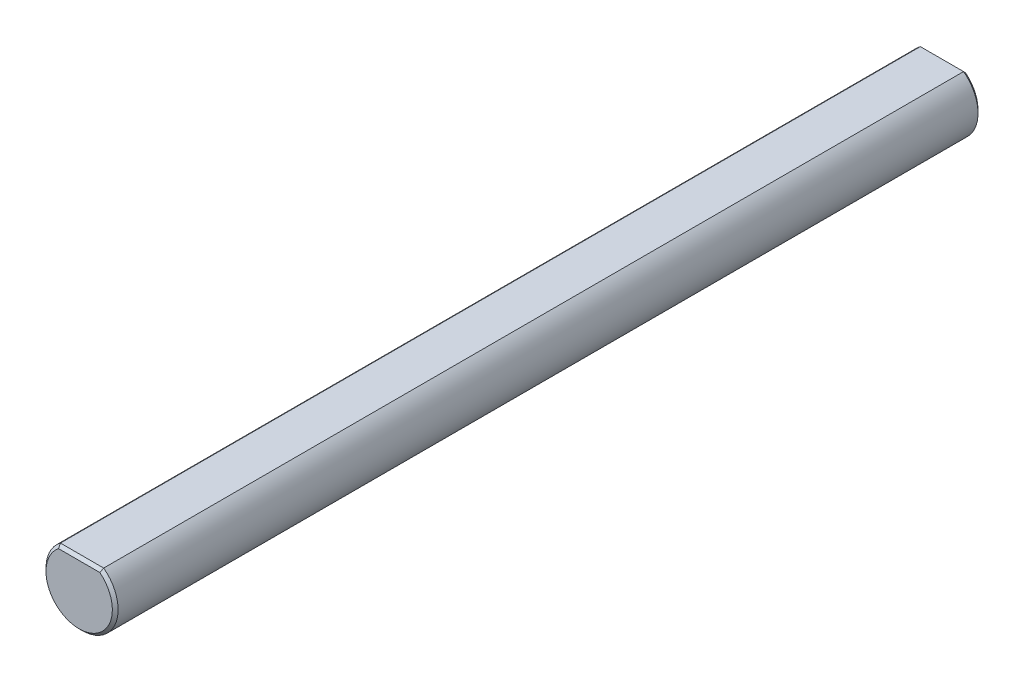
SolidWorks part; units mm, degrees
ref_plane "Front Plane" through (0, 0, 0) normal (0, 0, 1) x (1, 0, 0)
ref_plane "Top Plane" through (0, 0, 0) normal (0, 1, 0) x (1, 0, 0)
ref_plane "Right Plane" through (0, 0, 0) normal (1, 0, 0) x (0, 0, -1)
sketch "Sketch1" plane through (0, 0, 0) normal (0, 0, 1) x (1, 0, 0)
  line L1 (1.905, 2.54) -> (-1.905, 2.54)
  arc A0 (-1.905, 2.54) -> (1.905, 2.54) centre (0, 0) ccw
  dimension "D1" = 6.35
  dimension "D2" = 5.715
extrude "Boss-Extrude1" add sketch "Sketch1" along normal mid plane 76.2
chamfer "Chamfer1" distance 0.254 angle 45 4 edges at (0, 2.54, 38.1) (0, -3.175, 38.1) (0, 2.54, -38.1) (0, -3.175, -38.1)
